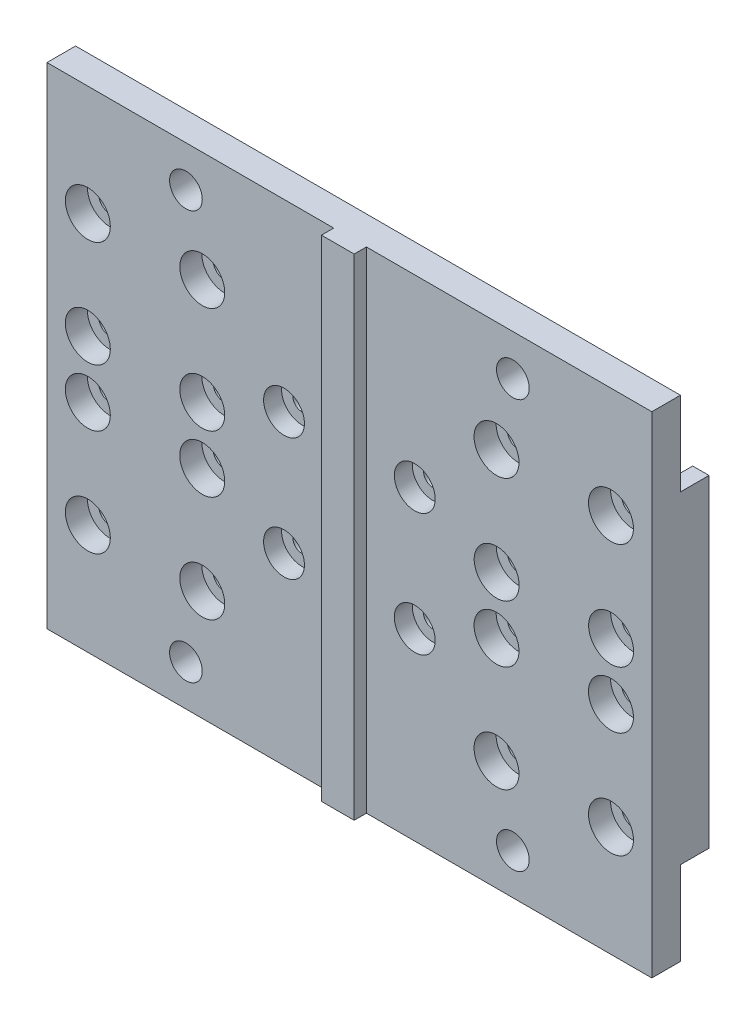
SolidWorks part; units mm, degrees
ref_plane "Plan de face" through (0, 0, 0) normal (0, 0, 1) x (1, 0, 0)
ref_plane "Plan de dessus" through (0, 0, 0) normal (0, 1, 0) x (1, 0, 0)
ref_plane "Plan de droite" through (0, 0, 0) normal (1, 0, 0) x (0, 0, -1)
sketch "Esquisse1" plane through (0, 0, 0) normal (0, 0, 1) x (1, 0, 0)
  line L0 (0, 80.3793) -> (0, -91.4076) construction
  line L1 (-74, 66.3924) -> (74, 66.3924)
  line L2 (-74, 66.3924) -> (-74, -53.6076)
  line L3 (-74, -53.6076) -> (74, -53.6076)
  line L4 (74, 66.3924) -> (74, -53.6076)
  line L5 (-70, 66.3924) -> (-70, -53.6076) construction
  line L6 (70, 66.3924) -> (70, -53.6076) construction
  line L7 (-30, 66.3924) -> (-30, -53.6076) construction
  line L8 (30, 66.3924) -> (30, -53.6076) construction
  line L9 (20, 66.3924) -> (20, -53.6076) construction
  line L10 (-20, 66.3924) -> (-20, -53.6076) construction
  line L11 (-64, -0.6076) -> (-64, -26.6076) construction
  line L12 (-36, 39.3924) -> (-36, -26.6076) construction
  line L13 (36, -0.6076) -> (36, -26.6076) construction
  line L14 (64, -0.6076) -> (64, -26.6076) construction
  line L15 (-46, 66.3924) -> (-46, -53.6076) construction
  line L16 (-14, 66.3924) -> (-14, -53.6076) construction
  line L17 (-46, 6.3924) -> (-87.0016, 6.3924) construction
  line L18 (46, 66.3924) -> (46, -53.6076) construction
  line L19 (14, 66.3924) -> (14, -53.6076) construction
  line L20 (46, 6.3924) -> (86.0513, 6.3924) construction
  line L21 (16, -53.6076) -> (16, 66.3924) construction
  line L22 (-16, -53.6076) -> (-16, 66.3924) construction
  circle A0 centre (-64, -0.6076) radius 2.5
  circle A1 centre (-36, 39.3924) radius 2.5
  circle A2 centre (-64, -26.6076) radius 2.5
  circle A3 centre (-36, -26.6076) radius 2.5
  circle A4 centre (36, -0.6076) radius 2.5
  circle A5 centre (64, -0.6076) radius 2.5
  circle A6 centre (36, -26.6076) radius 2.5
  circle A7 centre (64, -26.6076) radius 2.5
  circle A8 centre (-36, -0.6076) radius 2.5
  circle A9 centre (-64, 39.3924) radius 2.5
  circle A10 centre (16, 21.3924) radius 2
  circle A11 centre (16, -8.6076) radius 2
  circle A12 centre (-16, 21.3924) radius 2
  circle A13 centre (-16, -8.6076) radius 2
  circle A14 centre (-64, 13.3924) radius 2.5
  circle A15 centre (-36, 13.3924) radius 2.5
  circle A16 centre (36, 39.3924) radius 2.5
  circle A17 centre (36, 13.3924) radius 2.5
  circle A18 centre (64, 39.3924) radius 2.5
  circle A19 centre (64, 13.3924) radius 2.5
  dimension "D9" = 5
  dimension "D10" = 5
  dimension "D11" = 5
  dimension "D12" = 5
  dimension "D13" = 5
  dimension "D14" = 5
  dimension "D15" = 5
  dimension "D16" = 5
  dimension "D26" = 32
  dimension "D27" = 16
  dimension "D31" = 26
  dimension "D32" = 5
  dimension "D30" = 16
  dimension "D33" = 4
  dimension "D34" = 4
  dimension "D41" = 4
  dimension "D42" = 4
  dimension "D44" = 45
  dimension "D46" = 45
  dimension "D47" = 5
  dimension "D48" = 5
  dimension "D49" = 5
  dimension "D53" = 5
  dimension "D54" = 5
  dimension "D55" = 5
  dimension "D56" = 5
  dimension "D1" = 148
  dimension "D2" = 120
  dimension "D4" = 20
  dimension "D5" = 40
  dimension "D6" = 40
  dimension "D7" = 10
  dimension "D8" = 10
  dimension "D17" = 26
  dimension "D18" = 28
  dimension "D19" = 6
  dimension "D20" = 27
  dimension "D21" = 28
  dimension "D22" = 26
  dimension "D23" = 6
  dimension "D24" = 27
  dimension "D25" = 28
  dimension "D28" = 28
  dimension "D29" = 32
  dimension "D35" = 27
  dimension "D36" = 27
  dimension "D37" = 27
  dimension "D38" = 20
  dimension "D39" = 26
  dimension "D40" = 74
  dimension "D43" = 45
  dimension "D45" = 45
  dimension "D50" = 26
  dimension "D51" = 26
  dimension "D52" = 27
  dimension "D57" = 26
  dimension "D58" = 26
  dimension "D59" = 27
  dimension "D60" = 27
extrude "Extrusion1" add sketch "Esquisse1" along normal blind 4
sketch "Esquisse2" plane through (0, 0, 4) normal (0, 0, 1) x (1, 0, 0)
  line L0 (-74, 56.3924) -> (74, 56.3924) construction
  line L1 (-74, 66.3924) -> (-74, -53.6076) construction
  line L2 (74, -53.6076) -> (74, 66.3924) construction
  line L3 (-74, -43.6076) -> (74, -43.6076) construction
  line L4 (74, 66.3924) -> (-74, 66.3924) construction
  line L5 (-74, -53.6076) -> (74, -53.6076) construction
  line L6 (0, 66.3924) -> (0, -53.6076) construction
  circle A0 centre (-40, 56.3924) radius 4
  circle A1 centre (-40, -43.6076) radius 4
  circle A2 centre (40, 56.3924) radius 4
  circle A3 centre (40, -43.6076) radius 4
  dimension "D3" = 8
  dimension "D5" = 80
  dimension "D6" = 40
  dimension "D7" = 40
  dimension "D1" = 10
  dimension "D2" = 10
  dimension "D4" = 80
extrude "Enlèv. mat.-Extru.1" cut sketch "Esquisse2" against normal through all
sketch "Esquisse3" plane through (0, 0, 4) normal (0, 0, 1) x (1, 0, 0)
  line L1 (-74, 66.3924) -> (74, 66.3924)
  line L2 (-74, 66.3924) -> (-74, -53.6076)
  line L3 (-74, -53.6076) -> (74, -53.6076)
  line L4 (74, 66.3924) -> (74, -53.6076)
extrude "Boss.-Extru.1" add sketch "Esquisse3" along normal blind 3
hole_wizard "Chambrage pour vis à tête hexagonale M41" positions "Esquisse5" profile "Esquisse4" counterbore size "M4" standard "ISO" end condition through all
sketch "Esquisse5" plane through (0, 0, 7) normal (0, 0, 1) x (1, 0, 0)
  line L0 (0, 66.3924) -> (0, -53.6076) construction
  line L1 (74, 66.3924) -> (-74, 66.3924) construction
  line L2 (-74, -53.6076) -> (74, -53.6076) construction
  point P0 (-16, 21.3924)
  point P2 (16, 21.3924)
  point P4 (16, -8.6076)
  point P6 (-16, -8.6076)
  dimension "D1" = 16
  dimension "D2" = 16
  dimension "D3" = 16
  dimension "D4" = 16
  dimension "D5" = 45
  dimension "D6" = 45
  dimension "D7" = 45
  dimension "D8" = 45
sketch "Esquisse4" plane through (-16, 21.3924, 7) normal (1, 0, 0) x (0, -1, 0)
  line L0 (0, 0) -> (0, 7)
  line L1 (0, 7) -> (2.25, 7)
  line L3 (2.25, 7) -> (2.25, 4.4)
  line L4 (2.25, 4.4) -> (5, 4.4)
  line L5 (5, 4.4) -> (5, 0)
  line L7 (5, 0) -> (0, 0)
  line L11 (0, -6.35) -> (0, 107.95) construction
  dimension "Diamètre du perçage jusqu'au prochain" = 4.5
  dimension "Profondeur du perçage jusqu'au prochain" = 7
  dimension "Diamètre du chambrage" = 10
  dimension "Profondeur du chambrage" = 4.4
hole_wizard "Chambrage pour vis à tête hexagonale M51" positions "Esquisse7" profile "Esquisse6" counterbore size "M5" standard "ISO" end condition through all
sketch "Esquisse7" plane through (0, 0, 7) normal (0, 0, 1) x (1, 0, 0)
  line L0 (-74, 6.3924) -> (74, 6.3924) construction
  line L1 (-74, 66.3924) -> (-74, -53.6076) construction
  line L2 (74, -53.6076) -> (74, 66.3924) construction
  line L11 (0, 66.3924) -> (0, -53.6076) construction
  line L12 (74, 66.3924) -> (-74, 66.3924) construction
  line L13 (-74, -53.6076) -> (74, -53.6076) construction
  line L16 (-30, 66.3924) -> (-30, -53.6076) construction
  line L19 (30, 66.3924) -> (30, -53.6076) construction
  point P0 (-64, -0.6076)
  point P2 (-36, -0.6076)
  point P4 (-36, -26.6076)
  point P6 (-64, -26.6076)
  point P8 (36, -0.6076)
  point P10 (64, -0.6076)
  point P12 (64, -26.6076)
  point P14 (36, -26.6076)
  point P64 (-64, 39.3924)
  point P66 (-36, 39.3924)
  point P68 (-64.0005, 13.3924)
  point P70 (-36.0005, 13.3924)
  point P72 (36, 39.3924)
  point P74 (64, 39.3924)
  point P76 (36.0384, 13.3924)
  point P78 (64.0384, 13.3924)
  dimension "D1" = 30
  dimension "D2" = 30
  dimension "D3" = 33
  dimension "D4" = 33
  dimension "D5" = 26
  dimension "D6" = 26
  dimension "D7" = 33
  dimension "D8" = 26
  dimension "D9" = 33
  dimension "D10" = 26
  dimension "D11" = 6
  dimension "D12" = 6
  dimension "D13" = 28
  dimension "D14" = 28
  dimension "D15" = 6
  dimension "D16" = 6
  dimension "D17" = 28
  dimension "D18" = 28
  dimension "D19" = 28
  dimension "D20" = 28
  dimension "D21" = 28
  dimension "D22" = 28
  dimension "D23" = 26
  dimension "D24" = 26
  dimension "D25" = 6
  dimension "D26" = 6.0005
  dimension "D27" = 33
  dimension "D28" = 33
  dimension "D29" = 26
  dimension "D30" = 26
  dimension "D31" = 33
  dimension "D32" = 6
sketch "Esquisse6" plane through (-64, -0.6076, 7) normal (1, 0, 0) x (0, -1, 0)
  line L0 (0, 0) -> (0, 7)
  line L1 (0, 7) -> (2.75, 7)
  line L3 (2.75, 7) -> (2.75, 5.4)
  line L4 (2.75, 5.4) -> (5.5, 5.4)
  line L5 (5.5, 5.4) -> (5.5, 0)
  line L7 (5.5, 0) -> (0, 0)
  line L11 (0, -6.35) -> (0, 107.95) construction
  dimension "Diamètre du perçage jusqu'au prochain" = 5.5
  dimension "Profondeur du perçage jusqu'au prochain" = 7
  dimension "Diamètre du chambrage" = 11
  dimension "Profondeur du chambrage" = 5.4
sketch "Esquisse8" plane through (0, 0, 0) normal (0, 0, -1) x (-1, 0, 0)
  circle A0 centre (40, -43.6076) radius 4
  circle A1 centre (40, 56.3924) radius 4
  circle A2 centre (-40, 56.3924) radius 4
  circle A3 centre (-40, -43.6076) radius 4
extrude "Enlèv. mat.-Extru.2" cut sketch "Esquisse8" against normal through all
sketch "Esquisse9" plane through (0, 0, 0) normal (0, 0, -1) x (-1, 0, 0)
  line L0 (-74, 6.3924) -> (74, 6.3924) construction
  line L1 (-74, -53.6076) -> (-74, 66.3924) construction
  line L2 (74, 66.3924) -> (74, -53.6076) construction
  line L4 (-74, 66.3924) -> (74, 66.3924)
  line L5 (-74, 66.3924) -> (-74, -53.6076)
  line L6 (-74, -53.6076) -> (74, -53.6076)
  line L7 (74, 66.3924) -> (74, -53.6076)
  circle A0 centre (-64, -0.6076) radius 2.75
  circle A1 centre (-64, -26.6076) radius 2.75
  circle A2 centre (-36, -0.6076) radius 2.75
  circle A3 centre (-36, -26.6076) radius 2.75
  circle A4 centre (-16, 21.3924) radius 2.25
  circle A5 centre (16, 21.3924) radius 2.25
  circle A6 centre (-16, -8.6076) radius 2.25
  circle A7 centre (16, -8.6076) radius 2.25
  circle A8 centre (36, -0.6076) radius 2.75
  circle A9 centre (64, -0.6076) radius 2.75
  circle A10 centre (36, -26.6076) radius 2.75
  circle A11 centre (64, -26.6076) radius 2.75
  dimension "D1" = 120
  dimension "D2" = 60
extrude "Boss.-Extru.2" add sketch "Esquisse9" along normal blind 4
sketch "Esquisse11" plane through (0, 0, 7) normal (0, 0, 1) x (1, 0, 0)
  line L0 (74, 66.3924) -> (-74, 66.3924) construction
  line L1 (-3.8364, 66.3924) -> (4.1636, 66.3924)
  line L2 (-3.8364, 66.3924) -> (-3.8364, -53.6076)
  line L3 (-3.8364, -53.6076) -> (4.1636, -53.6076)
  line L4 (4.1636, 66.3924) -> (4.1636, -53.6076)
  line L5 (-74, -53.6076) -> (74, -53.6076) construction
  line L6 (0.1636, 38.0166) -> (0.1636, -65.5655) construction
  dimension "D1" = 4
  dimension "D2" = 8
extrude "Boss.-Extru.4" add sketch "Esquisse11" along normal blind 3
sketch "Esquisse12" plane through (0, 0, 0) normal (0, 0, 1) x (1, 0, 0)
  circle A0 centre (-40, 56.3924) radius 4
  circle A1 centre (40, 56.3924) radius 4
  circle A2 centre (40, -43.6076) radius 4
  circle A3 centre (-40, -43.6076) radius 4
extrude "Enlèv. mat.-Extru.3" cut sketch "Esquisse12" against normal through all
sketch "Esquisse13" plane through (0, 0, 0) normal (0, 0, 1) x (1, 0, 0)
  circle A0 centre (-64, 39.3924) radius 2.75
  circle A1 centre (-36, 39.3924) radius 2.75
  circle A2 centre (-36.0005, 13.3924) radius 2.75
  circle A3 centre (-64.0005, 13.3924) radius 2.75
  circle A4 centre (36, 39.3924) radius 2.75
  circle A5 centre (64, 39.3924) radius 2.75
  circle A6 centre (36.0384, 13.3924) radius 2.75
  circle A7 centre (64.0384, 13.3924) radius 2.75
extrude "Enlèv. mat.-Extru.4" cut sketch "Esquisse13" against normal through all
sketch "Esquisse14" plane through (0, 0, -4) normal (0, 0, -1) x (-1, 0, 0)
  line L0 (-74, 66.3924) -> (-74, -53.6076) construction
  line L1 (74, -53.6076) -> (-74, -53.6076)
  line L2 (74, -53.6076) -> (74, -33.1076)
  line L3 (74, -33.1076) -> (-74, -33.1076)
  line L4 (-74, -53.6076) -> (-74, -33.1076)
  line L6 (74, 66.3924) -> (-74, 66.3924)
  line L7 (74, 66.3924) -> (74, 45.8924)
  line L8 (74, 45.8924) -> (-74, 45.8924)
  line L9 (-74, 66.3924) -> (-74, 45.8924)
  dimension "D1" = 20.5
  dimension "D2" = 20.5
extrude "Enlèv. mat.-Extru.5" cut sketch "Esquisse14" against normal blind 4
sketch "Esquisse15" plane through (0, 0, -4) normal (0, 0, -1) x (-1, 0, 0)
  line L0 (74, -33.1076) -> (-74, -33.1076) construction
  line L1 (-74, 45.8924) -> (-70, 45.8924)
  line L2 (-74, 45.8924) -> (-74, -33.1076)
  line L3 (-74, -33.1076) -> (-70, -33.1076)
  line L4 (-70, 45.8924) -> (-70, -33.1076)
  line L5 (-74, 45.8924) -> (74, 45.8924) construction
  line L6 (-30, 45.8924) -> (-20, 45.8924)
  line L7 (-30, 45.8924) -> (-30, -33.1076)
  line L8 (-30, -33.1076) -> (-20, -33.1076)
  line L9 (-20, 45.8924) -> (-20, -33.1076)
  line L10 (74, -33.1076) -> (-74, -33.1076) construction
  line L11 (20, 45.8924) -> (30, 45.8924)
  line L12 (20, 45.8924) -> (20, -33.1076)
  line L13 (20, -33.1076) -> (30, -33.1076)
  line L14 (30, 45.8924) -> (30, -33.1076)
  line L16 (70, 45.8924) -> (74, 45.8924)
  line L17 (70, 45.8924) -> (70, -33.1076)
  line L18 (70, -33.1076) -> (74, -33.1076)
  line L19 (74, 45.8924) -> (74, -33.1076)
  dimension "D1" = 4
  dimension "D2" = 4
  dimension "D3" = 10
  dimension "D4" = 10
  dimension "D5" = 40
  dimension "D6" = 40
extrude "Boss.-Extru.5" add sketch "Esquisse15" along normal blind 3
